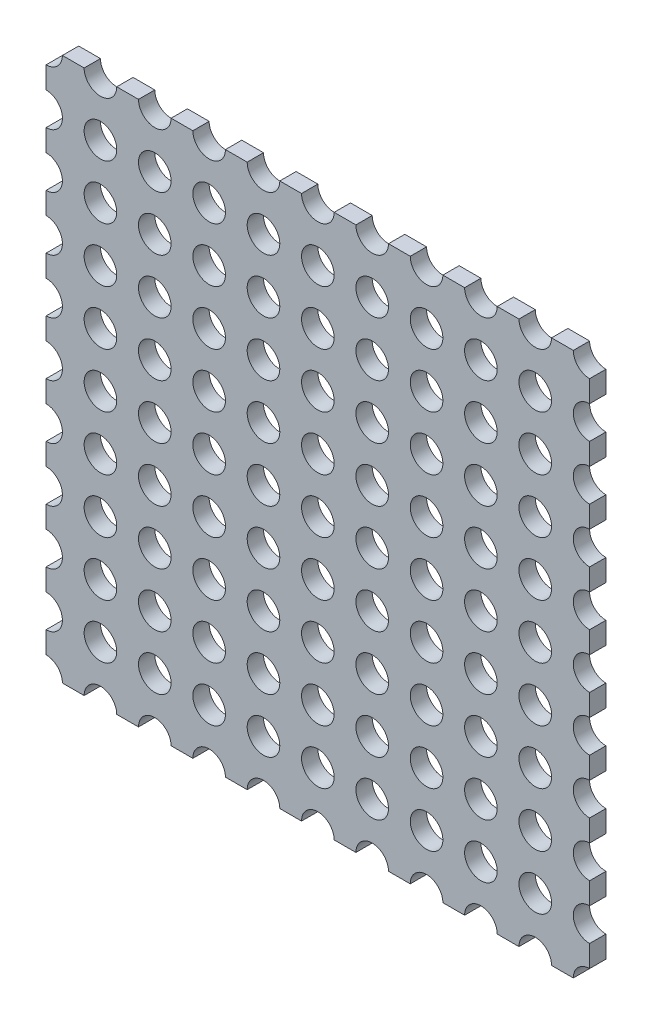
SolidWorks part; units mm, degrees
ref_plane "Płaszczyzna przednia" through (0, 0, 0) normal (0, 0, 1) x (1, 0, 0)
ref_plane "Płaszczyzna górna" through (0, 0, 0) normal (0, 1, 0) x (1, 0, 0)
ref_plane "Płaszczyzna prawa" through (0, 0, 0) normal (1, 0, 0) x (0, 0, -1)
sketch "Szkic1" plane through (0, 0, 0) normal (0, 0, 1) x (1, 0, 0)
  line L1 (-250, -250) -> (250, -250)
  line L2 (-250, -250) -> (-250, 250)
  line L3 (-250, 250) -> (250, 250)
  line L4 (250, -250) -> (250, 250)
  line L5 (-250, -250) -> (250, 250) construction
  line L6 (-250, 250) -> (250, -250) construction
  point P0 (0, 0)
  dimension "L" = 500
  dimension "H" = 500
extrude "Dodanie-wyciągnięcie1" add sketch "Szkic1" along normal blind 15
sketch "Szkic2" plane through (0, 0, 0) normal (0, 0, 1) x (1, 0, 0)
  circle A0 centre (-250, 250) radius 15
  dimension "D1" = 30
extrude "Wytnij-wyciągnięcie1" cut sketch "Szkic2" along normal blind 15
pattern_linear "Szyk liniowy1" count 11 spacing 50 along (1, 0, 0) count 11 spacing 50 along (0, -1, 0) of "Wytnij-wyciągnięcie1"
